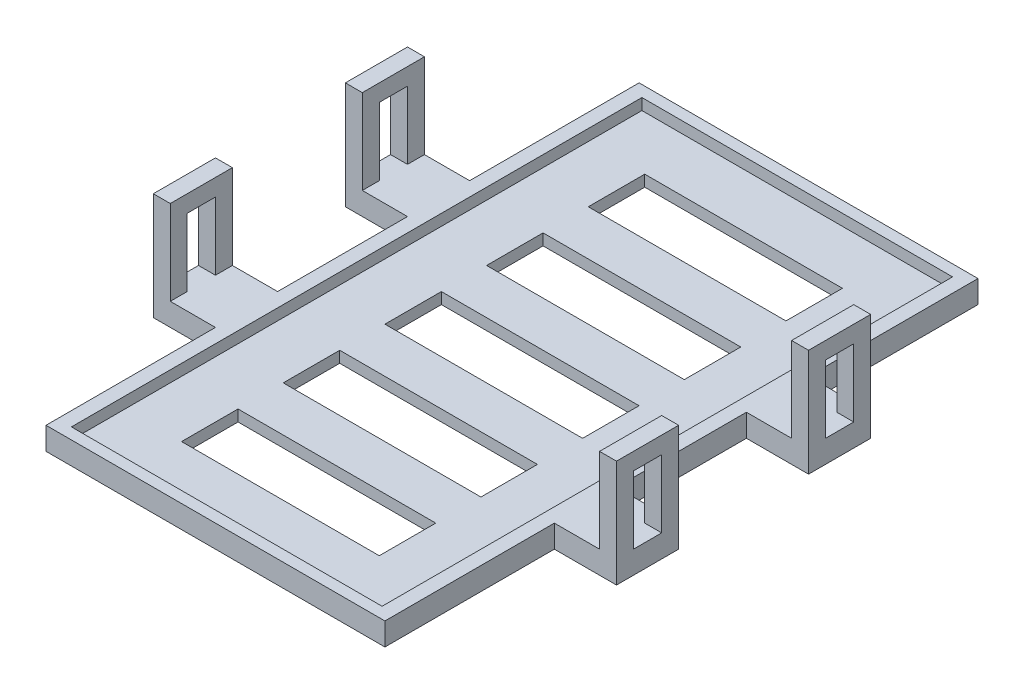
SolidWorks part; units mm, degrees
ref_plane "Alzado" through (0, 0, 0) normal (0, 0, 1) x (1, 0, 0)
ref_plane "Planta" through (0, 0, 0) normal (0, 1, 0) x (1, 0, 0)
ref_plane "Vista lateral" through (0, 0, 0) normal (1, 0, 0) x (0, 0, -1)
sketch "Croquis1" plane through (0, 0, 0) normal (0, 1, 0) x (1, 0, 0)
  line L0 (30, -52.5) -> (30, -22.5)
  line L1 (-30, 52.5) -> (30, 52.5)
  line L2 (30, -22.5) -> (30, -11.5) construction
  line L3 (-30, -52.5) -> (30, -52.5)
  line L4 (30, 11.5) -> (30, 22.5) construction
  line L5 (-30, 52.5) -> (30, -52.5) construction
  line L6 (-30, -52.5) -> (30, 52.5) construction
  line L7 (30, -22.5) -> (41, -22.5)
  line L8 (41, -22.5) -> (41, -11.5)
  line L9 (41, -11.5) -> (30, -11.5)
  line L10 (30, -11.5) -> (30, 11.5)
  line L11 (30, 11.5) -> (41, 11.5)
  line L12 (41, 11.5) -> (41, 22.5)
  line L13 (41, 22.5) -> (30, 22.5)
  line L14 (30, 22.5) -> (30, 52.5)
  line L15 (-30, 52.5) -> (-30, 22.5)
  line L16 (-30, 22.5) -> (-41, 22.5)
  line L17 (-41, 22.5) -> (-41, 11.5)
  line L18 (-41, 11.5) -> (-30, 11.5)
  line L19 (-30, 11.5) -> (-30, -11.5)
  line L20 (-30, -11.5) -> (-41, -11.5)
  line L21 (-41, -11.5) -> (-41, -22.5)
  line L22 (-41, -22.5) -> (-30, -22.5)
  line L23 (-30, -22.5) -> (-30, -52.5)
  line L24 (-30, 11.5) -> (-30, 22.5) construction
  line L25 (-30, -22.5) -> (-30, -11.5) construction
  point P0 (0, 0)
  dimension "D1" = 23
  dimension "D2" = 60
  dimension "D3" = 11
  dimension "D4" = 11
  dimension "D5" = 30
extrude "Saliente-Extruir1" add sketch "Croquis1" along normal blind 4
sketch "Croquis2" plane through (0, 4, 0) normal (0, 1, 0) x (1, 0, 0)
  line L0 (30, 52.5) -> (-30, 52.5) construction
  line L1 (-27.5, 50.5) -> (27.5, 50.5)
  line L2 (-27.5, 50.5) -> (-27.5, -50.5)
  line L3 (-27.5, -50.5) -> (27.5, -50.5)
  line L4 (27.5, 50.5) -> (27.5, -50.5)
  line L5 (-27.5, 50.5) -> (27.5, -50.5) construction
  line L6 (-27.5, -50.5) -> (27.5, 50.5) construction
  point P0 (0, 0)
  dimension "D1" = 2
  dimension "D2" = 55
extrude "Cortar-Extruir1" cut sketch "Croquis2" against normal blind 2
sketch "Croquis12" plane through (0, 4, 0) normal (0, 1, 0) x (1, 0, 0)
  line L0 (-41, 11.5) -> (-30, 11.5) construction
  line L1 (-41, 22.5) -> (-38, 22.5)
  line L2 (-41, 22.5) -> (-41, 11.5)
  line L3 (-41, 11.5) -> (-38, 11.5)
  line L4 (-38, 22.5) -> (-38, 11.5)
  line L5 (-41, -22.5) -> (-30, -22.5) construction
  line L6 (-41, -11.5) -> (-38, -11.5)
  line L7 (-41, -11.5) -> (-41, -22.5)
  line L8 (-41, -22.5) -> (-38, -22.5)
  line L9 (-38, -11.5) -> (-38, -22.5)
  line L10 (30, -22.5) -> (41, -22.5) construction
  line L11 (41, -11.5) -> (38, -11.5)
  line L12 (41, -11.5) -> (41, -22.5)
  line L13 (41, -22.5) -> (38, -22.5)
  line L14 (38, -11.5) -> (38, -22.5)
  line L15 (30, 11.5) -> (41, 11.5) construction
  line L16 (41, 22.5) -> (38, 22.5)
  line L17 (41, 22.5) -> (41, 11.5)
  line L18 (41, 11.5) -> (38, 11.5)
  line L19 (38, 22.5) -> (38, 11.5)
  dimension "D1" = 3
extrude "Saliente-Extruir2" add sketch "Croquis12" along normal blind 15
sketch "Croquis13" plane through (38, 0, 0) normal (-1, 0, 0) x (0, 0, 1)
  line L0 (-22.5, 4) -> (-11.5, 4) construction
  line L1 (-19.5, 4) -> (-14.5, 4)
  line L2 (-19.5, 4) -> (-19.5, 16)
  line L3 (-19.5, 16) -> (-14.5, 16)
  line L4 (-14.5, 4) -> (-14.5, 16)
  line L5 (-19.5, 4) -> (-22.5, 4) construction
  line L6 (-14.5, 4) -> (-11.5, 4) construction
  line L8 (-19.5, 16) -> (-19.5, 19) construction
  line L9 (-22.5, 19) -> (-11.5, 19) construction
  dimension "D1" = 3
extrude "Cortar-Extruir8" cut sketch "Croquis13" against normal through all and the other way through all
sketch "Croquis14" plane through (38, 0, 0) normal (-1, 0, 0) x (0, 0, 1)
  line L0 (11.5, 4) -> (22.5, 4) construction
  line L1 (14.5, 4) -> (19.5, 4)
  line L2 (14.5, 4) -> (14.5, 16)
  line L3 (14.5, 16) -> (19.5, 16)
  line L4 (19.5, 4) -> (19.5, 16)
  line L5 (14.5, 16) -> (14.5, 19) construction
  line L6 (11.5, 19) -> (22.5, 19) construction
  line L7 (14.5, 4) -> (11.5, 4) construction
  line L8 (19.5, 4) -> (22.5, 4) construction
  dimension "D1" = 3
extrude "Cortar-Extruir9" cut sketch "Croquis14" against normal through all and the other way through all
sketch "Croquis15" plane through (0, 0, 0) normal (0, 1, 0) x (1, 0, 0)
  line L0 (-17.5, -31) -> (-17.5, -23) construction
  line L1 (17.5, 5) -> (-17.5, 5)
  line L2 (17.5, 5) -> (17.5, -5)
  line L3 (17.5, -5) -> (-17.5, -5)
  line L4 (-17.5, 5) -> (-17.5, -5)
  line L5 (17.5, 5) -> (-17.5, -5) construction
  line L6 (17.5, -5) -> (-17.5, 5) construction
  line L7 (17.5, -13) -> (-17.5, -13)
  line L8 (17.5, -13) -> (17.5, -23)
  line L9 (17.5, -23) -> (-17.5, -23)
  line L10 (-17.5, -13) -> (-17.5, -23)
  line L11 (17.5, -31) -> (-17.5, -31)
  line L12 (17.5, -31) -> (17.5, -41)
  line L13 (17.5, -41) -> (-17.5, -41)
  line L14 (-17.5, -31) -> (-17.5, -41)
  line L15 (17.5, 13) -> (-17.5, 13)
  line L16 (17.5, 13) -> (17.5, 23)
  line L17 (17.5, 23) -> (-17.5, 23)
  line L18 (-17.5, 13) -> (-17.5, 23)
  line L19 (-17.5, 31) -> (17.5, 31)
  line L20 (-17.5, 31) -> (-17.5, 41)
  line L21 (-17.5, 41) -> (17.5, 41)
  line L22 (17.5, 31) -> (17.5, 41)
  line L23 (-17.5, -13) -> (-17.5, -5) construction
  line L24 (-17.5, 5) -> (-17.5, 13) construction
  line L25 (-17.5, 23) -> (-17.5, 31) construction
  line L26 (-27.5, 50.5) -> (-27.5, -50.5) construction
  point P0 (0, 0)
  dimension "D1" = 10
  dimension "D2" = 8
  dimension "D3" = 10
extrude "Cortar-Extruir10" cut sketch "Croquis15" along normal through all
